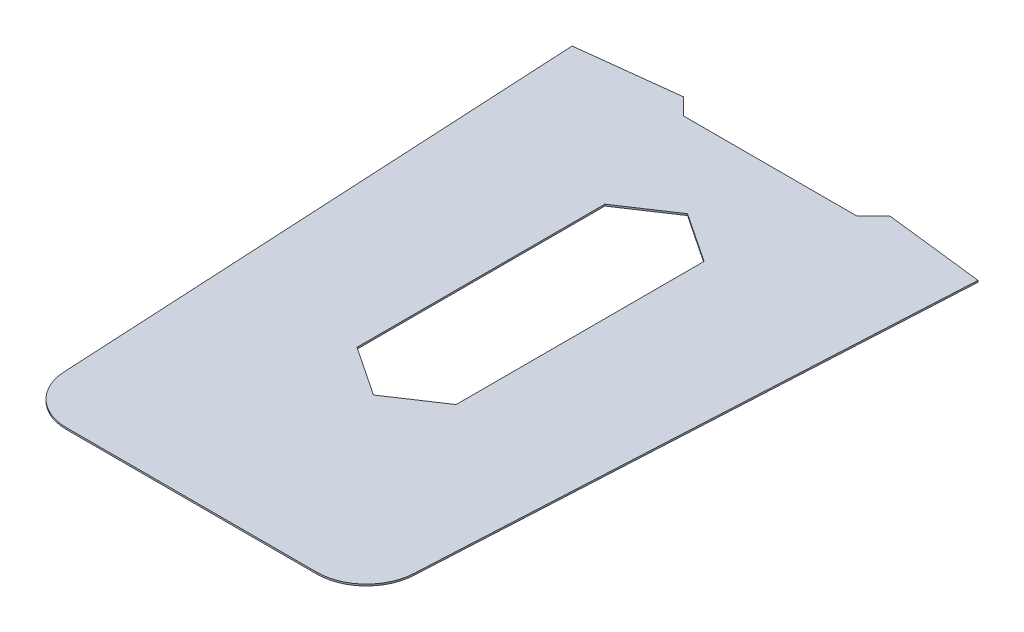
SolidWorks part; units mm, degrees
ref_plane "Front Plane" through (0, 0, 0) normal (0, 0, 1) x (1, 0, 0)
ref_plane "Top Plane" through (0, 0, 0) normal (0, 1, 0) x (1, 0, 0)
ref_plane "Right Plane" through (0, 0, 0) normal (1, 0, 0) x (0, 0, -1)
sketch "Sketch1" plane through (0, 0, 0) normal (0, 1, 0) x (1, 0, 0)
  line L0 (-38.1, 95.25) -> (0, 120.65)
  line L1 (-38.1, 95.25) -> (38.1, 95.25) construction
  line L2 (-38.1, 95.25) -> (-38.1, -95.25)
  line L3 (-38.1, -95.25) -> (38.1, -95.25) construction
  line L4 (38.1, 95.25) -> (38.1, -95.25)
  line L5 (-38.1, 95.25) -> (38.1, -95.25) construction
  line L6 (-38.1, -95.25) -> (38.1, 95.25) construction
  line L7 (0, 120.65) -> (38.1, 95.25)
  line L8 (-38.1, -95.25) -> (0, -120.65)
  line L9 (0, -120.65) -> (38.1, -95.25)
  line L10 (0, -120.65) -> (0, -260.35) construction
  line L11 (0, 120.65) -> (0, 184.15) construction
  line L12 (0, -120.65) -> (139.7, -120.65) construction
  line L13 (0, -120.65) -> (-139.7, -120.65) construction
  line L14 (0, 120.65) -> (152.4, 120.65) construction
  line L15 (0, 120.65) -> (-152.4, 120.65) construction
  line L16 (-152.4, 120.65) -> (-139.7, -120.65)
  line L17 (-139.7, -120.65) -> (-134.2472, -224.2525)
  line L18 (152.4, 120.65) -> (139.7, -120.65)
  line L19 (139.7, -120.65) -> (134.2472, -224.2525)
  line L20 (96.1999, -260.35) -> (0, -260.35)
  line L21 (0, -260.35) -> (-96.1999, -260.35)
  line L22 (0, 184.15) -> (-66.675, 184.15)
  line L23 (0, 184.15) -> (66.675, 184.15)
  line L24 (66.675, 184.15) -> (79.375, 196.85)
  line L25 (-66.675, 184.15) -> (-79.375, 196.85)
  line L26 (-79.375, 196.85) -> (-155.9396, 187.9028)
  line L27 (-155.9396, 187.9028) -> (-152.4, 120.65)
  line L28 (79.375, 196.85) -> (155.9396, 187.9028)
  line L29 (155.9396, 187.9028) -> (152.4, 120.65)
  arc A0 (134.2472, -224.2525) -> (96.1999, -260.35) centre (96.1999, -222.25) cw
  arc A1 (-134.2472, -224.2525) -> (-96.1999, -260.35) centre (-96.1999, -222.25) ccw
  point P0 (0, 0)
  point P20 (96.1999, 196.8374)
  point P27 (90.8152, 201.6903)
  point P28 (0, 0)
  point P29 (-156.2373, 193.5586)
  point P30 (-156.187, 192.6037)
  point P31 (-155.9396, 187.9028)
  dimension "D8" = 38.1
  dimension "D1" = 190.5
  dimension "D2" = 76.2
  dimension "D3" = 25.4
  dimension "D4" = 139.7
  dimension "D5" = 63.5
  dimension "D6" = 139.7
  dimension "D7" = 152.4
  dimension "D9" = 133.35
  dimension "D10" = 158.75
  dimension "D11" = 12.7
extrude "Boss-Extrude1" add sketch "Sketch1" along normal blind 1.27
